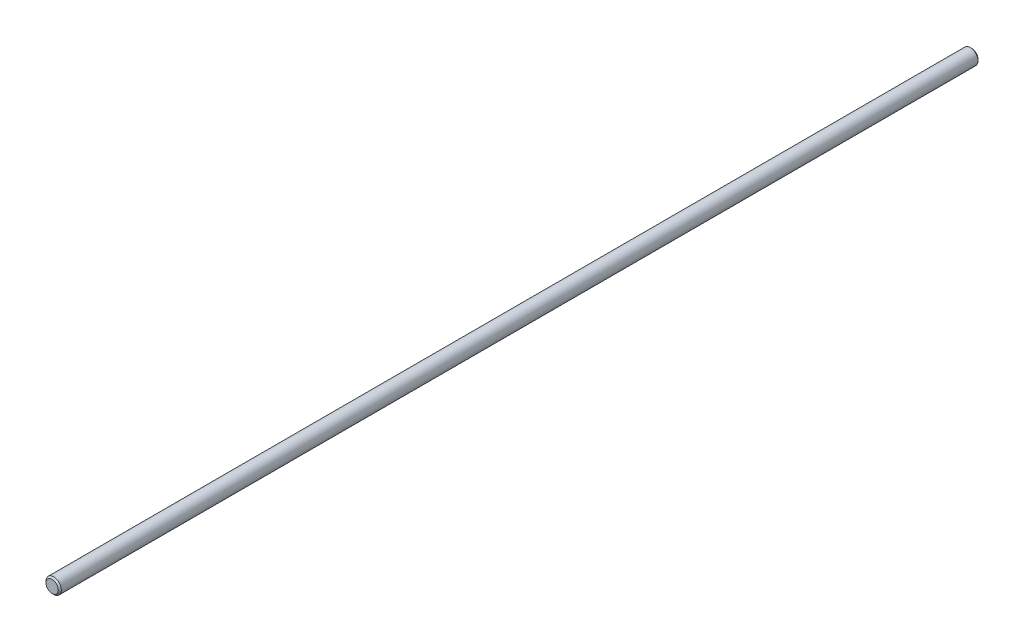
SolidWorks part; units mm, degrees
material "AISI 304"
ref_plane "Front Plane" through (0, 0, 0) normal (0, 0, 1) x (1, 0, 0)
ref_plane "Top Plane" through (0, 0, 0) normal (0, 1, 0) x (1, 0, 0)
ref_plane "Right Plane" through (0, 0, 0) normal (1, 0, 0) x (0, 0, -1)
sketch "Sketch1" plane through (0, 0, 0) normal (0, 0, 1) x (1, 0, 0)
  circle A0 centre (0, 0) radius 2.5
  dimension "D1" = 5
extrude "Boss-Extrude1" add sketch "Sketch1" against normal blind 300
cosmetic thread "Cosmetic Thread1" parameters "D2"=4.11
chamfer "Chamfer1" distance 0.5 angle 45 2 edges at (2.5, 0, -300) (2.5, 0, 0)
